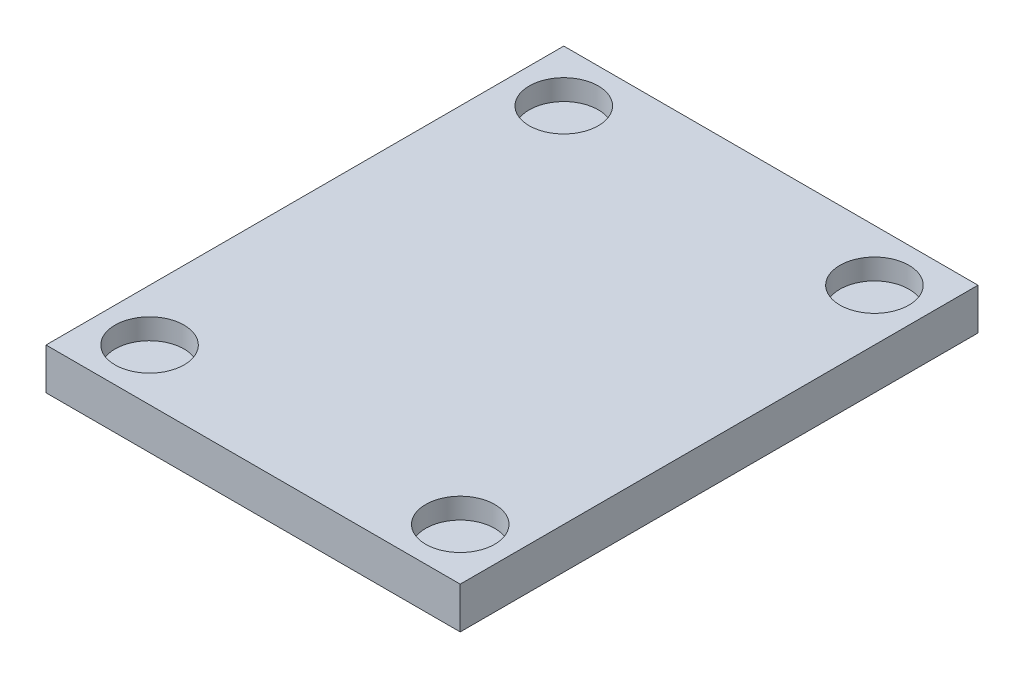
SolidWorks part; units mm, degrees
ref_plane "Front Plane" through (0, 0, 0) normal (0, 0, 1) x (1, 0, 0)
ref_plane "Top Plane" through (0, 0, 0) normal (0, 1, 0) x (1, 0, 0)
ref_plane "Right Plane" through (0, 0, 0) normal (1, 0, 0) x (0, 0, -1)
sketch "Sketch1" plane through (0, 0, 0) normal (0, 0, 1) x (1, 0, 0)
  line L1 (-30, 3) -> (30, 3)
  line L2 (-30, 3) -> (-30, -3)
  line L3 (-30, -3) -> (30, -3)
  line L4 (30, 3) -> (30, -3)
  line L5 (0, -3) -> (0, 3) construction
  line L6 (-30, 0) -> (30, 0) construction
  point P0 (0, 0)
  dimension "D1" = 6
  dimension "D2" = 60
extrude "Boss-Extrude1" add sketch "Sketch1" along normal blind 75
sketch "Sketch2" plane through (0, 3, 0) normal (0, 1, 0) x (1, 0, 0)
  line L1 (30, -75) -> (22.5, -75)
  line L2 (30, -75) -> (30, -67.5)
  line L3 (30, -67.5) -> (22.5, -67.5)
  line L4 (22.5, -75) -> (22.5, -67.5)
  line L5 (-30, -75) -> (-22.5, -75)
  line L6 (-30, -75) -> (-30, -67.5)
  line L7 (-30, -67.5) -> (-22.5, -67.5)
  line L8 (-22.5, -75) -> (-22.5, -67.5)
  line L9 (30, 0) -> (22.5, 0)
  line L10 (30, 0) -> (30, -7.5)
  line L11 (30, -7.5) -> (22.5, -7.5)
  line L12 (22.5, 0) -> (22.5, -7.5)
  line L13 (-30, 0) -> (-22.5, 0)
  line L14 (-30, 0) -> (-30, -7.5)
  line L15 (-30, -7.5) -> (-22.5, -7.5)
  line L16 (-22.5, 0) -> (-22.5, -7.5)
  point P20 (-30, -3.75)
  dimension "D1" = 7.5
  dimension "D2" = 7.5
  dimension "D3" = 7.5
  dimension "D4" = 7.5
  dimension "D5" = 7.5
  dimension "D6" = 7.5
  dimension "D7" = 7.5
  dimension "D8" = 7.5
sketch "Sketch3" plane through (0, 3, 0) normal (0, 1, 0) x (1, 0, 0)
  circle A0 centre (22.5, -67.5) radius 5
  circle A1 centre (-22.5, -67.5) radius 5
  circle A2 centre (-22.5, -7.5) radius 5
  circle A3 centre (22.5, -7.5) radius 5
extrude "Cut-Extrude2" cut sketch "Sketch3" against normal blind 3
